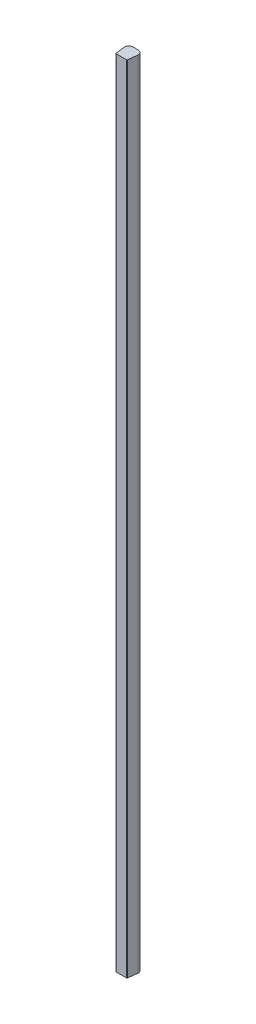
SolidWorks part; units mm, degrees
ref_plane "Front Plane" through (0, 0, 0) normal (0, 0, 1) x (1, 0, 0)
ref_plane "Top Plane" through (0, 0, 0) normal (0, 1, 0) x (1, 0, 0)
ref_plane "Right Plane" through (0, 0, 0) normal (1, 0, 0) x (0, 0, -1)
sketch "Sketch1" plane through (0, 0, 0) normal (0, 1, 0) x (1, 0, 0)
  line L1 (13.6302, 10) -> (23.6302, 10)
  line L3 (0.2982, -2.4286) -> (3.2992, -26.87)
  line L4 (5.2843, -28.6263) -> (31.976, -28.6263)
  line L5 (36.9706, -2.3598) -> (33.9611, -26.87)
  arc A0 (2.1102, 4.6358) -> (13.6302, 10) centre (12.6577, -2.9636) cw
  arc A1 (34.9994, 4.9193) -> (23.6302, 10) centre (24.6588, -2.9592) ccw
  arc A2 (36.9706, -2.3598) -> (34.9994, 4.9193) centre (27.0451, -1.1411) ccw
  arc A3 (0.2982, -2.4286) -> (2.1102, 4.6358) centre (10.2237, -1.2099) cw
  arc A4 (31.976, -28.6263) -> (33.9611, -26.87) centre (31.976, -26.6263) ccw
  arc A5 (3.2992, -26.87) -> (5.2843, -28.6263) centre (5.2843, -26.6263) ccw
  point P5 (2.911, -28.8286)
  point P10 (33.8055, -28.5469)
  point P11 (5.3794, 5.7623)
  point P12 (4.3868, 2.3991)
  point P13 (6.5004, 7.599)
  point P14 (0, 0)
  point P15 (4.5124, 4.9762)
  point P16 (0, 0)
  point P17 (0, 0)
  point P18 (0, 0)
  point P19 (10.4858, 0)
  point P20 (18.6302, 10)
  point P21 (18.6302, -28.6263)
  point P24 (37.2797, 0.1575)
  point P27 (0, 0)
  point P30 (33.7455, -28.6263)
  dimension "D3" = 10
  dimension "D7" = 13
  dimension "D8" = 10
  dimension "D9" = 2
  dimension "D1" = 37.28
  dimension "D2" = 29
  dimension "D4" = 10
  dimension "D5" = 83
  dimension "D6" = 83
extrude "Boss-Extrude1" add sketch "Sketch1" along normal blind 2133.6
